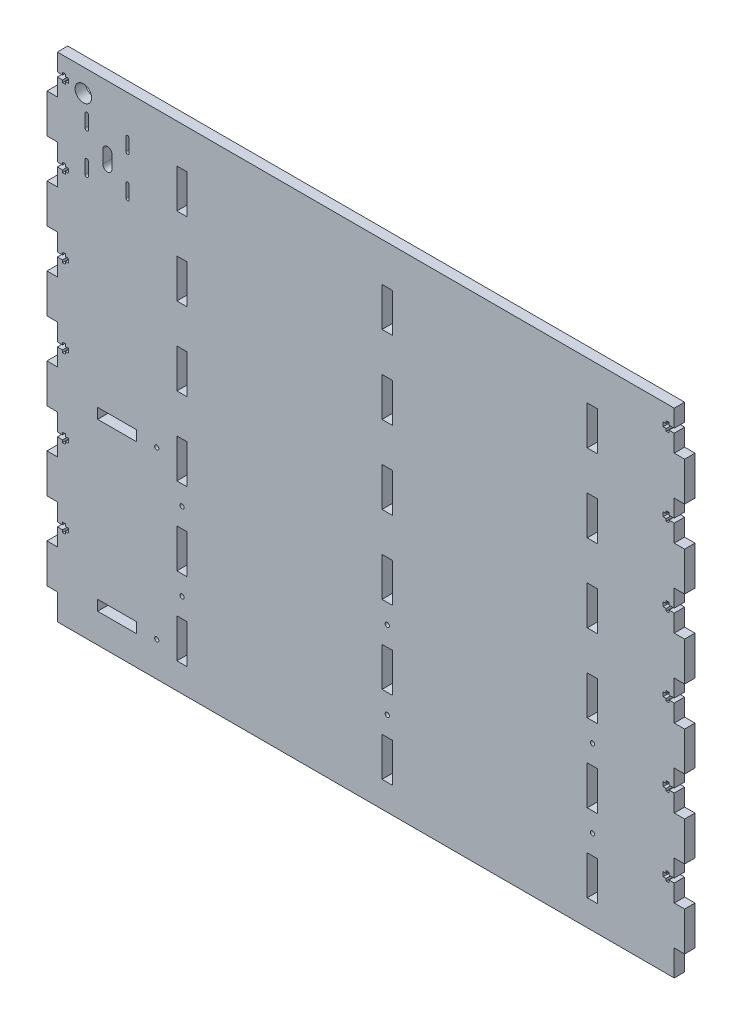
SolidWorks part; units mm, degrees
material "Acrylic (Medium-high impact)"
ref_plane "Front Plane" through (0, 0, 0) normal (0, 0, 1) x (1, 0, 0)
ref_plane "Top Plane" through (0, 0, 0) normal (0, 1, 0) x (1, 0, 0)
ref_plane "Right Plane" through (0, 0, 0) normal (1, 0, 0) x (0, 0, -1)
sketch "Sketch1" plane through (0, 0, 0) normal (0, 0, 1) x (1, 0, 0)
  line L0 (38.5456, 332.8173) -> (38.5456, 322.8173) construction
  line L1 (0, 0) -> (475, 0)
  line L2 (0, 0) -> (0, 380)
  line L3 (0, 380) -> (475, 380)
  line L4 (475, 0) -> (475, 380)
  line L5 (42.0456, 332.8173) -> (42.0456, 322.8173)
  line L6 (35.0456, 332.8173) -> (35.0456, 322.8173)
  line L7 (54.0456, 350) -> (54.0456, 340) construction
  line L8 (55.3456, 350) -> (55.3456, 340)
  line L9 (52.7456, 350) -> (52.7456, 340)
  line L10 (22.645, 350) -> (22.645, 340) construction
  line L11 (23.945, 350) -> (23.945, 340)
  line L12 (21.345, 350) -> (21.345, 340)
  line L13 (54.0456, 319) -> (54.0456, 309) construction
  line L14 (55.3456, 319) -> (55.3456, 309)
  line L15 (52.7456, 319) -> (52.7456, 309)
  line L16 (22.645, 319) -> (22.645, 309) construction
  line L17 (23.945, 319) -> (23.945, 309)
  line L18 (21.345, 319) -> (21.345, 309)
  line L20 (61, 30.5669) -> (31, 30.5669)
  line L21 (61, 30.5669) -> (61, 22.5669)
  line L22 (61, 22.5669) -> (31, 22.5669)
  line L23 (31, 30.5669) -> (31, 22.5669)
  line L24 (61, 158.5669) -> (31, 158.5669)
  line L25 (61, 158.5669) -> (61, 150.5669)
  line L26 (61, 150.5669) -> (31, 150.5669)
  line L27 (31, 158.5669) -> (31, 150.5669)
  line L28 (100, 350) -> (92, 350)
  line L29 (100, 350) -> (100, 320)
  line L30 (100, 320) -> (92, 320)
  line L31 (92, 350) -> (92, 320)
  line L87 (258, 350) -> (258, 320)
  line L88 (258, 350) -> (250, 350)
  line L89 (250, 350) -> (250, 320)
  line L90 (258, 320) -> (250, 320)
  line L91 (416, 350) -> (416, 320)
  line L92 (416, 350) -> (408, 350)
  line L93 (408, 350) -> (408, 320)
  line L94 (416, 320) -> (408, 320)
  line L95 (100, 290) -> (100, 260)
  line L96 (100, 290) -> (92, 290)
  line L97 (92, 290) -> (92, 260)
  line L98 (100, 260) -> (92, 260)
  line L99 (258, 290) -> (258, 260)
  line L100 (258, 290) -> (250, 290)
  line L101 (250, 290) -> (250, 260)
  line L102 (258, 260) -> (250, 260)
  line L103 (416, 290) -> (416, 260)
  line L104 (416, 290) -> (408, 290)
  line L105 (408, 290) -> (408, 260)
  line L106 (416, 260) -> (408, 260)
  line L107 (100, 230) -> (100, 200)
  line L108 (100, 230) -> (92, 230)
  line L109 (92, 230) -> (92, 200)
  line L110 (100, 200) -> (92, 200)
  line L111 (258, 230) -> (258, 200)
  line L112 (258, 230) -> (250, 230)
  line L113 (250, 230) -> (250, 200)
  line L114 (258, 200) -> (250, 200)
  line L115 (416, 230) -> (416, 200)
  line L116 (416, 230) -> (408, 230)
  line L117 (408, 230) -> (408, 200)
  line L118 (416, 200) -> (408, 200)
  line L119 (100, 170) -> (100, 140)
  line L120 (100, 170) -> (92, 170)
  line L121 (92, 170) -> (92, 140)
  line L122 (100, 140) -> (92, 140)
  line L123 (258, 170) -> (258, 140)
  line L124 (258, 170) -> (250, 170)
  line L125 (250, 170) -> (250, 140)
  line L126 (258, 140) -> (250, 140)
  line L127 (416, 170) -> (416, 140)
  line L128 (416, 170) -> (408, 170)
  line L129 (408, 170) -> (408, 140)
  line L130 (416, 140) -> (408, 140)
  line L131 (100, 110) -> (100, 80)
  line L132 (100, 110) -> (92, 110)
  line L133 (92, 110) -> (92, 80)
  line L134 (100, 80) -> (92, 80)
  line L135 (258, 110) -> (258, 80)
  line L136 (258, 110) -> (250, 110)
  line L137 (250, 110) -> (250, 80)
  line L138 (258, 80) -> (250, 80)
  line L139 (416, 110) -> (416, 80)
  line L140 (416, 110) -> (408, 110)
  line L141 (408, 110) -> (408, 80)
  line L142 (416, 80) -> (408, 80)
  line L143 (100, 50) -> (100, 20)
  line L144 (100, 50) -> (92, 50)
  line L145 (92, 50) -> (92, 20)
  line L146 (100, 20) -> (92, 20)
  line L147 (258, 50) -> (258, 20)
  line L148 (258, 50) -> (250, 50)
  line L149 (250, 50) -> (250, 20)
  line L150 (258, 20) -> (250, 20)
  line L151 (416, 50) -> (416, 20)
  line L152 (416, 50) -> (408, 50)
  line L153 (408, 50) -> (408, 20)
  line L154 (416, 20) -> (408, 20)
  arc A0 (42.0456, 332.8173) -> (35.0456, 332.8173) centre (38.5456, 332.8173) ccw
  arc A1 (35.0456, 322.8173) -> (42.0456, 322.8173) centre (38.5456, 322.8173) ccw
  arc A2 (55.3456, 350) -> (52.7456, 350) centre (54.0456, 350) ccw
  arc A3 (52.7456, 340) -> (55.3456, 340) centre (54.0456, 340) ccw
  arc A4 (23.945, 350) -> (21.345, 350) centre (22.645, 350) ccw
  arc A5 (21.345, 340) -> (23.945, 340) centre (22.645, 340) ccw
  arc A6 (55.3456, 319) -> (52.7456, 319) centre (54.0456, 319) ccw
  arc A7 (52.7456, 309) -> (55.3456, 309) centre (54.0456, 309) ccw
  arc A8 (23.945, 319) -> (21.345, 319) centre (22.645, 319) ccw
  arc A9 (21.345, 309) -> (23.945, 309) centre (22.645, 309) ccw
  circle A10 centre (20, 362.5) radius 6.35
  circle A11 centre (76.5, 154.5669) radius 1.65
  circle A12 centre (76.5, 26.5669) radius 1.65
  circle A13 centre (96, 125) radius 1.65
  circle A14 centre (254, 125) radius 1.65
  circle A15 centre (412, 125) radius 1.65
  circle A16 centre (96, 65) radius 1.65
  circle A17 centre (254, 65) radius 1.65
  circle A18 centre (412, 65) radius 1.65
  point P8 (38.5456, 327.8173)
  point P13 (54.0456, 345)
  point P31 (22.645, 345)
  point P38 (54.0456, 314)
  point P50 (22.645, 314)
  dimension "D4" = 3.5
  dimension "D6" = 10
  dimension "D3" = 1.3
  dimension "D5" = 10
  dimension "D11" = 12.7
  dimension "D13" = 3.3
  dimension "D23" = 3.3
  dimension "D1" = 475
  dimension "D2" = 380
  dimension "D7" = 30
  dimension "D8" = 15.5
  dimension "D9" = 17.5
  dimension "D10" = 20
  dimension "D12" = 15.5
  dimension "D14" = 92
  dimension "D15" = 8
  dimension "D16" = 30
  dimension "D17" = 30
  dimension "D22" = 3
  dimension "D25" = 65
  dimension "D18" = 3
  dimension "D19" = 6
  dimension "D21" = 2
  dimension "D24" = 2
extrude "Boss-Extrude1" add sketch "Sketch1" along normal blind 8
sketch "Sketch2" plane through (0, 0, 8) normal (0, 0, 1) x (1, 0, 0)
  line L0 (0, 380) -> (0, 0) construction
  line L1 (0, 350) -> (-8, 350)
  line L2 (0, 350) -> (0, 320)
  line L3 (0, 320) -> (-8, 320)
  line L4 (-8, 350) -> (-8, 320)
  line L5 (475, 380) -> (0, 380) construction
  line L6 (483, 50) -> (483, 20)
  line L7 (475, 20) -> (483, 20)
  line L8 (475, 50) -> (475, 20)
  line L9 (475, 50) -> (483, 50)
  line L10 (483, 110) -> (483, 80)
  line L11 (475, 80) -> (483, 80)
  line L12 (475, 110) -> (475, 80)
  line L13 (475, 110) -> (483, 110)
  line L14 (483, 170) -> (483, 140)
  line L15 (475, 140) -> (483, 140)
  line L16 (475, 170) -> (475, 140)
  line L17 (475, 170) -> (483, 170)
  line L18 (483, 230) -> (483, 200)
  line L19 (475, 200) -> (483, 200)
  line L20 (475, 230) -> (475, 200)
  line L21 (475, 230) -> (483, 230)
  line L22 (237.5, 380) -> (237.5, 0) construction
  line L23 (0, 0) -> (475, 0) construction
  line L24 (483, 290) -> (483, 260)
  line L25 (475, 260) -> (483, 260)
  line L26 (475, 290) -> (475, 260)
  line L27 (475, 290) -> (483, 290)
  line L28 (483, 350) -> (483, 320)
  line L29 (475, 320) -> (483, 320)
  line L30 (475, 350) -> (475, 320)
  line L31 (475, 350) -> (483, 350)
  line L44 (0, 290) -> (-8, 290)
  line L45 (0, 290) -> (0, 260)
  line L46 (0, 260) -> (-8, 260)
  line L47 (-8, 290) -> (-8, 260)
  line L48 (0, 230) -> (-8, 230)
  line L49 (0, 230) -> (0, 200)
  line L50 (0, 200) -> (-8, 200)
  line L51 (-8, 230) -> (-8, 200)
  line L52 (0, 170) -> (-8, 170)
  line L53 (0, 170) -> (0, 140)
  line L54 (0, 140) -> (-8, 140)
  line L55 (-8, 170) -> (-8, 140)
  line L56 (0, 110) -> (-8, 110)
  line L57 (0, 110) -> (0, 80)
  line L58 (0, 80) -> (-8, 80)
  line L59 (-8, 110) -> (-8, 80)
  line L60 (0, 50) -> (-8, 50)
  line L61 (0, 50) -> (0, 20)
  line L62 (0, 20) -> (-8, 20)
  line L63 (-8, 50) -> (-8, 20)
  dimension "D1" = 30
  dimension "D2" = 30
  dimension "D3" = 8
  dimension "D4" = 6
extrude "Boss-Extrude2" add sketch "Sketch2" against normal blind 8
sketch "Sketch3" plane through (0, 0, 0) normal (0, 0, -1) x (-1, 0, 0)
  line L0 (0, 366.65) -> (-4, 366.65)
  line L1 (0, 380) -> (0, 350) construction
  line L2 (-4, 366.65) -> (-4, 368.5)
  line L3 (-4, 368.5) -> (-6.2, 368.5)
  line L4 (-6.2, 368.5) -> (-6.2, 366.65)
  line L5 (-6.2, 366.65) -> (-8.5, 366.65)
  line L6 (0, 365) -> (-8.5, 365) construction
  line L7 (-8.5, 366.65) -> (-8.5, 363.35)
  line L8 (-6.2, 363.35) -> (-8.5, 363.35)
  line L9 (-6.2, 361.5) -> (-6.2, 363.35)
  line L10 (-4, 361.5) -> (-6.2, 361.5)
  line L11 (-4, 363.35) -> (-4, 361.5)
  line L12 (0, 363.35) -> (-4, 363.35)
  line L13 (0, 366.65) -> (0, 363.35)
  line L14 (0, 306.65) -> (-4, 306.65)
  line L15 (-4, 306.65) -> (-4, 308.5)
  line L16 (-4, 308.5) -> (-6.2, 308.5)
  line L17 (-6.2, 308.5) -> (-6.2, 306.65)
  line L18 (-6.2, 306.65) -> (-8.5, 306.65)
  line L19 (-8.5, 306.65) -> (-8.5, 303.35)
  line L20 (-6.2, 303.35) -> (-8.5, 303.35)
  line L21 (-6.2, 301.5) -> (-6.2, 303.35)
  line L22 (-4, 301.5) -> (-6.2, 301.5)
  line L23 (-4, 303.35) -> (-4, 301.5)
  line L24 (0, 303.35) -> (-4, 303.35)
  line L25 (0, 306.65) -> (0, 303.35)
  line L36 (0, 305) -> (-8.5, 305) construction
  line L37 (0, 246.65) -> (-4, 246.65)
  line L38 (-4, 246.65) -> (-4, 248.5)
  line L39 (-4, 248.5) -> (-6.2, 248.5)
  line L40 (-6.2, 248.5) -> (-6.2, 246.65)
  line L41 (-6.2, 246.65) -> (-8.5, 246.65)
  line L42 (-8.5, 246.65) -> (-8.5, 243.35)
  line L43 (-6.2, 243.35) -> (-8.5, 243.35)
  line L44 (-6.2, 241.5) -> (-6.2, 243.35)
  line L45 (-4, 241.5) -> (-6.2, 241.5)
  line L46 (-4, 243.35) -> (-4, 241.5)
  line L47 (0, 243.35) -> (-4, 243.35)
  line L48 (0, 246.65) -> (0, 243.35)
  line L59 (0, 245) -> (-8.5, 245) construction
  line L60 (0, 186.65) -> (-4, 186.65)
  line L61 (-4, 186.65) -> (-4, 188.5)
  line L62 (-4, 188.5) -> (-6.2, 188.5)
  line L63 (-6.2, 188.5) -> (-6.2, 186.65)
  line L64 (-6.2, 186.65) -> (-8.5, 186.65)
  line L65 (-8.5, 186.65) -> (-8.5, 183.35)
  line L66 (-6.2, 183.35) -> (-8.5, 183.35)
  line L67 (-6.2, 181.5) -> (-6.2, 183.35)
  line L68 (-4, 181.5) -> (-6.2, 181.5)
  line L69 (-4, 183.35) -> (-4, 181.5)
  line L70 (0, 183.35) -> (-4, 183.35)
  line L71 (0, 186.65) -> (0, 183.35)
  line L74 (-237.5, 380) -> (-237.5, 0) construction
  line L75 (-475, 380) -> (0, 380) construction
  line L76 (0, 0) -> (-475, 0) construction
  line L95 (0, 185) -> (-8.5, 185) construction
  line L96 (0, 126.65) -> (-4, 126.65)
  line L97 (-4, 126.65) -> (-4, 128.5)
  line L98 (-4, 128.5) -> (-6.2, 128.5)
  line L99 (-6.2, 128.5) -> (-6.2, 126.65)
  line L100 (-6.2, 126.65) -> (-8.5, 126.65)
  line L101 (-8.5, 126.65) -> (-8.5, 123.35)
  line L102 (-6.2, 123.35) -> (-8.5, 123.35)
  line L103 (-6.2, 121.5) -> (-6.2, 123.35)
  line L104 (-4, 121.5) -> (-6.2, 121.5)
  line L105 (-4, 123.35) -> (-4, 121.5)
  line L106 (0, 123.35) -> (-4, 123.35)
  line L107 (0, 126.65) -> (0, 123.35)
  line L118 (0, 125) -> (-8.5, 125) construction
  line L119 (0, 66.65) -> (-4, 66.65)
  line L120 (-4, 66.65) -> (-4, 68.5)
  line L121 (-4, 68.5) -> (-6.2, 68.5)
  line L122 (-6.2, 68.5) -> (-6.2, 66.65)
  line L123 (-6.2, 66.65) -> (-8.5, 66.65)
  line L124 (-8.5, 66.65) -> (-8.5, 63.35)
  line L125 (-6.2, 63.35) -> (-8.5, 63.35)
  line L126 (-6.2, 61.5) -> (-6.2, 63.35)
  line L127 (-4, 61.5) -> (-6.2, 61.5)
  line L128 (-4, 63.35) -> (-4, 61.5)
  line L129 (0, 63.35) -> (-4, 63.35)
  line L130 (0, 66.65) -> (0, 63.35)
  line L141 (0, 65) -> (-8.5, 65) construction
  line L162 (-475, 65) -> (-466.5, 65) construction
  line L163 (-475, 125) -> (-466.5, 125) construction
  line L164 (-475, 185) -> (-466.5, 185) construction
  line L165 (-475, 245) -> (-466.5, 245) construction
  line L166 (-475, 305) -> (-466.5, 305) construction
  line L167 (-475, 365) -> (-466.5, 365) construction
  line L168 (-475, 363.35) -> (-471, 363.35)
  line L169 (-471, 363.35) -> (-471, 361.5)
  line L170 (-471, 361.5) -> (-468.8, 361.5)
  line L171 (-468.8, 361.5) -> (-468.8, 363.35)
  line L172 (-468.8, 363.35) -> (-466.5, 363.35)
  line L173 (-468.8, 366.65) -> (-466.5, 366.65)
  line L174 (-468.8, 368.5) -> (-468.8, 366.65)
  line L175 (-471, 368.5) -> (-468.8, 368.5)
  line L176 (-471, 366.65) -> (-471, 368.5)
  line L177 (-475, 366.65) -> (-471, 366.65)
  line L188 (-475, 63.35) -> (-471, 63.35)
  line L189 (-471, 63.35) -> (-471, 61.5)
  line L190 (-471, 61.5) -> (-468.8, 61.5)
  line L191 (-468.8, 61.5) -> (-468.8, 63.35)
  line L192 (-468.8, 63.35) -> (-466.5, 63.35)
  line L193 (-468.8, 66.65) -> (-466.5, 66.65)
  line L194 (-468.8, 68.5) -> (-468.8, 66.65)
  line L195 (-471, 68.5) -> (-468.8, 68.5)
  line L196 (-471, 66.65) -> (-471, 68.5)
  line L197 (-475, 66.65) -> (-471, 66.65)
  line L198 (-475, 66.65) -> (-475, 63.35)
  line L204 (-466.5, 66.65) -> (-466.5, 63.35)
  line L210 (-475, 123.35) -> (-471, 123.35)
  line L211 (-471, 123.35) -> (-471, 121.5)
  line L212 (-471, 121.5) -> (-468.8, 121.5)
  line L213 (-468.8, 121.5) -> (-468.8, 123.35)
  line L214 (-468.8, 123.35) -> (-466.5, 123.35)
  line L215 (-468.8, 126.65) -> (-466.5, 126.65)
  line L216 (-468.8, 128.5) -> (-468.8, 126.65)
  line L217 (-471, 128.5) -> (-468.8, 128.5)
  line L218 (-471, 126.65) -> (-471, 128.5)
  line L219 (-475, 126.65) -> (-471, 126.65)
  line L220 (-475, 126.65) -> (-475, 123.35)
  line L226 (-466.5, 126.65) -> (-466.5, 123.35)
  line L232 (-475, 183.35) -> (-471, 183.35)
  line L233 (-471, 183.35) -> (-471, 181.5)
  line L234 (-471, 181.5) -> (-468.8, 181.5)
  line L235 (-468.8, 181.5) -> (-468.8, 183.35)
  line L236 (-468.8, 183.35) -> (-466.5, 183.35)
  line L237 (-468.8, 186.65) -> (-466.5, 186.65)
  line L238 (-468.8, 188.5) -> (-468.8, 186.65)
  line L239 (-471, 188.5) -> (-468.8, 188.5)
  line L250 (-471, 186.65) -> (-471, 188.5)
  line L251 (-475, 186.65) -> (-471, 186.65)
  line L252 (-475, 186.65) -> (-475, 183.35)
  line L258 (-466.5, 186.65) -> (-466.5, 183.35)
  line L264 (-475, 243.35) -> (-471, 243.35)
  line L265 (-471, 243.35) -> (-471, 241.5)
  line L266 (-471, 241.5) -> (-468.8, 241.5)
  line L267 (-468.8, 241.5) -> (-468.8, 243.35)
  line L268 (-468.8, 243.35) -> (-466.5, 243.35)
  line L269 (-468.8, 246.65) -> (-466.5, 246.65)
  line L270 (-468.8, 248.5) -> (-468.8, 246.65)
  line L271 (-471, 248.5) -> (-468.8, 248.5)
  line L272 (-471, 246.65) -> (-471, 248.5)
  line L273 (-475, 246.65) -> (-471, 246.65)
  line L274 (-475, 246.65) -> (-475, 243.35)
  line L280 (-466.5, 246.65) -> (-466.5, 243.35)
  line L286 (-475, 303.35) -> (-471, 303.35)
  line L287 (-471, 303.35) -> (-471, 301.5)
  line L288 (-471, 301.5) -> (-468.8, 301.5)
  line L289 (-468.8, 301.5) -> (-468.8, 303.35)
  line L290 (-468.8, 303.35) -> (-466.5, 303.35)
  line L291 (-468.8, 306.65) -> (-466.5, 306.65)
  line L292 (-468.8, 308.5) -> (-468.8, 306.65)
  line L293 (-471, 308.5) -> (-468.8, 308.5)
  line L294 (-471, 306.65) -> (-471, 308.5)
  line L295 (-475, 306.65) -> (-471, 306.65)
  line L296 (-475, 306.65) -> (-475, 303.35)
  line L302 (-466.5, 306.65) -> (-466.5, 303.35)
  line L308 (-475, 366.65) -> (-475, 363.35)
  line L314 (-466.5, 366.65) -> (-466.5, 363.35)
  line L320 (0, 366.65) -> (-4, 366.65) [skipped]
  line L321 (-6.2, 366.65) -> (-8.5, 366.65) [skipped]
  line L322 (-4, 63.35) -> (-4, 61.5) [skipped]
  line L323 (-4, 66.65) -> (-4, 68.5) [skipped]
  line L324 (-4, 123.35) -> (-4, 121.5) [skipped]
  line L325 (-4, 126.65) -> (-4, 128.5) [skipped]
  line L326 (-4, 183.35) -> (-4, 181.5) [skipped]
  line L327 (-4, 186.65) -> (-4, 188.5) [skipped]
  line L328 (-4, 243.35) -> (-4, 241.5) [skipped]
  line L329 (-4, 246.65) -> (-4, 248.5) [skipped]
  line L330 (-4, 303.35) -> (-4, 301.5) [skipped]
  line L331 (-4, 306.65) -> (-4, 308.5) [skipped]
  line L332 (-4, 363.35) -> (-4, 361.5) [skipped]
  line L333 (-4, 366.65) -> (-4, 368.5) [skipped]
  line L334 (-4, 368.5) -> (-6.2, 368.5) [skipped]
  line L335 (-6.2, 368.5) -> (-6.2, 366.65) [skipped]
  line L336 (-6.2, 361.5) -> (-6.2, 363.35) [skipped]
  line L337 (-6.2, 308.5) -> (-6.2, 306.65) [skipped]
  line L338 (-6.2, 301.5) -> (-6.2, 303.35) [skipped]
  line L339 (-6.2, 248.5) -> (-6.2, 246.65) [skipped]
  line L340 (-6.2, 241.5) -> (-6.2, 243.35) [skipped]
  line L341 (-6.2, 188.5) -> (-6.2, 186.65) [skipped]
  line L342 (-6.2, 181.5) -> (-6.2, 183.35) [skipped]
  line L343 (-6.2, 128.5) -> (-6.2, 126.65) [skipped]
  line L344 (-6.2, 121.5) -> (-6.2, 123.35) [skipped]
  line L345 (-6.2, 68.5) -> (-6.2, 66.65) [skipped]
  line L346 (-6.2, 61.5) -> (-6.2, 63.35) [skipped]
  line L347 (0, 363.35) -> (-4, 363.35) [skipped]
  line L348 (-6.2, 363.35) -> (-8.5, 363.35) [skipped]
  line L349 (-4, 361.5) -> (-6.2, 361.5) [skipped]
  line L350 (0, 306.65) -> (-4, 306.65) [skipped]
  line L351 (-6.2, 306.65) -> (-8.5, 306.65) [skipped]
  line L352 (-4, 308.5) -> (-6.2, 308.5) [skipped]
  line L353 (0, 303.35) -> (-4, 303.35) [skipped]
  line L354 (-6.2, 303.35) -> (-8.5, 303.35) [skipped]
  line L355 (-4, 301.5) -> (-6.2, 301.5) [skipped]
  line L356 (0, 246.65) -> (-4, 246.65) [skipped]
  line L357 (-6.2, 246.65) -> (-8.5, 246.65) [skipped]
  line L358 (-4, 248.5) -> (-6.2, 248.5) [skipped]
  line L359 (0, 243.35) -> (-4, 243.35) [skipped]
  line L360 (-6.2, 243.35) -> (-8.5, 243.35) [skipped]
  line L361 (-4, 241.5) -> (-6.2, 241.5) [skipped]
  line L362 (0, 186.65) -> (-4, 186.65) [skipped]
  line L363 (-6.2, 186.65) -> (-8.5, 186.65) [skipped]
  line L364 (-4, 188.5) -> (-6.2, 188.5) [skipped]
  line L365 (0, 183.35) -> (-4, 183.35) [skipped]
  line L366 (-6.2, 183.35) -> (-8.5, 183.35) [skipped]
  line L367 (-4, 181.5) -> (-6.2, 181.5) [skipped]
  line L368 (0, 126.65) -> (-4, 126.65) [skipped]
  line L369 (-6.2, 126.65) -> (-8.5, 126.65) [skipped]
  line L370 (-4, 128.5) -> (-6.2, 128.5) [skipped]
  line L371 (0, 123.35) -> (-4, 123.35) [skipped]
  line L372 (-6.2, 123.35) -> (-8.5, 123.35) [skipped]
  line L373 (-4, 121.5) -> (-6.2, 121.5) [skipped]
  line L374 (0, 66.65) -> (-4, 66.65) [skipped]
  line L375 (-6.2, 66.65) -> (-8.5, 66.65) [skipped]
  line L376 (-4, 68.5) -> (-6.2, 68.5) [skipped]
  line L377 (0, 63.35) -> (-4, 63.35) [skipped]
  line L378 (-6.2, 63.35) -> (-8.5, 63.35) [skipped]
  line L379 (-4, 61.5) -> (-6.2, 61.5) [skipped]
  dimension "D1" = 3.3
  dimension "D2" = 2.2
  dimension "D3" = 4
  dimension "D4" = 2.3
  dimension "D5" = 7
extrude "Cut-Extrude1" cut sketch "Sketch3" against normal through all
